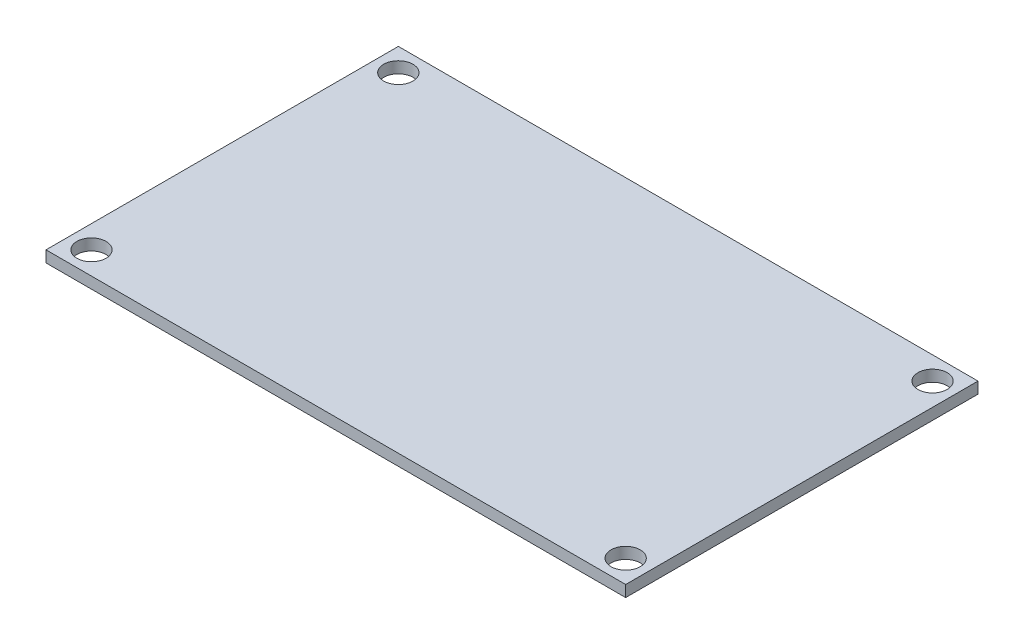
SolidWorks part; units mm, degrees
material "6061-T6 (SS)"
ref_plane "Front Plane" through (0, 0, 0) normal (0, 0, 1) x (1, 0, 0)
ref_plane "Top Plane" through (0, 0, 0) normal (0, 1, 0) x (1, 0, 0)
ref_plane "Right Plane" through (0, 0, 0) normal (1, 0, 0) x (0, 0, -1)
sketch "Sketch1" plane through (0, 0, 0) normal (0, 1, 0) x (1, 0, 0)
  line L1 (-32.385, -19.685) -> (32.385, -19.685)
  line L2 (-32.385, -19.685) -> (-32.385, 19.685)
  line L3 (-32.385, 19.685) -> (32.385, 19.685)
  line L4 (32.385, -19.685) -> (32.385, 19.685)
  line L5 (-32.385, -19.685) -> (32.385, 19.685) construction
  line L6 (-32.385, 19.685) -> (32.385, -19.685) construction
  point P0 (0, 0)
  dimension "D1" = 64.77
  dimension "D2" = 39.37
extrude "Boss-Extrude1" add sketch "Sketch1" along normal blind 1.27
hole_wizard "#4 Clearance Hole1" positions "Sketch2" profile "Sketch3" hole size "#4" standard "ANSI Inch"
sketch "Sketch2" plane through (0, 1.27, 0) normal (0, 1, 0) x (1, 0, 0)
  line L0 (-32.385, -19.685) -> (32.385, -19.685) construction
  line L1 (-32.385, 19.685) -> (-32.385, -19.685) construction
  line L2 (32.385, 19.685) -> (-32.385, 19.685) construction
  line L3 (32.385, -19.685) -> (32.385, 19.685) construction
  point P0 (-29.845, 17.145)
  point P2 (-29.845, -17.145)
  point P4 (29.845, -17.145)
  point P6 (29.845, 17.145)
  dimension "D1" = 2.54
  dimension "D2" = 2.54
  dimension "D3" = 2.54
  dimension "D4" = 2.54
sketch "Sketch3" plane through (-29.845, 1.27, -17.145) normal (1, 0, 0) x (0, 0, 1)
  line L0 (0, 0) -> (0, 8.5752)
  line L1 (0, 8.5752) -> (1.6319, 7.5946)
  line L2 (1.6319, 7.5946) -> (1.6319, 0)
  line L5 (1.6319, 0) -> (0, 0)
  line L10 (0, 8.5752) -> (-1.632, 7.5946) construction
  line L11 (0, -6.35) -> (0, 107.95) construction
  dimension "Hole Dia." = 3.2639
  dimension "Hole Depth" = 7.5946
  dimension "Drill Angle" = 118
